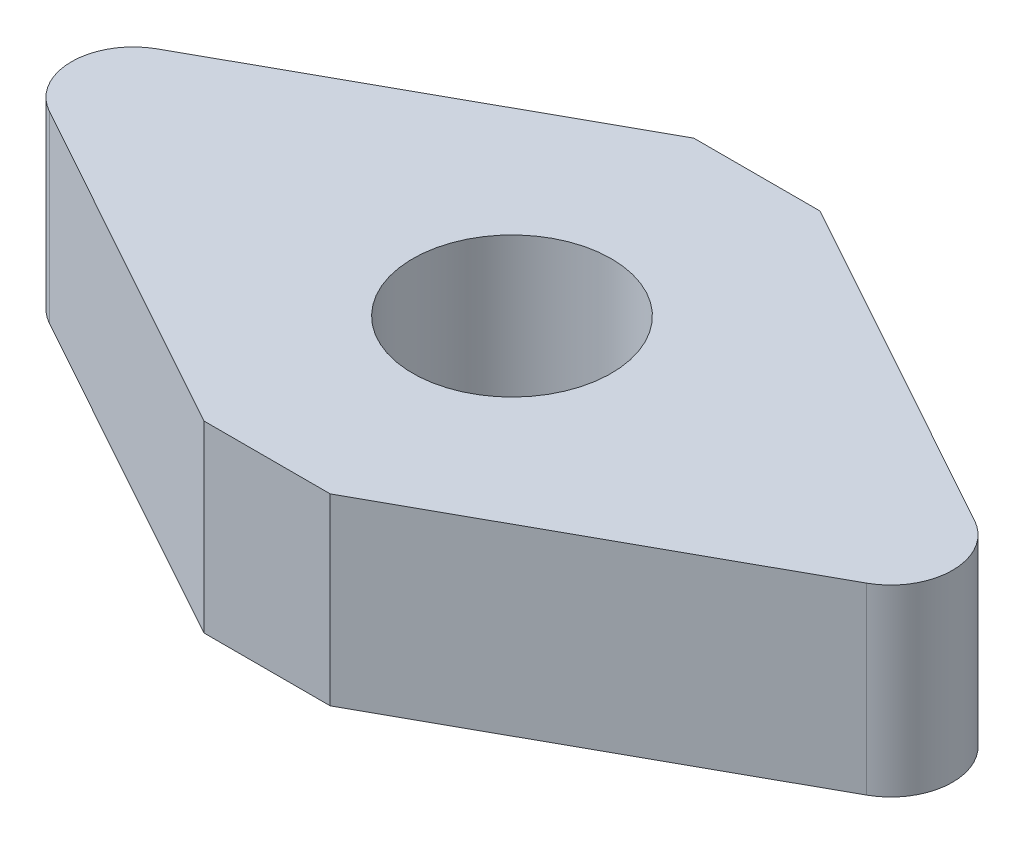
SolidWorks part; units mm, degrees
ref_plane "Ebene vorne" through (0, 0, 0) normal (0, 0, 1) x (1, 0, 0)
ref_plane "Ebene oben" through (0, 0, 0) normal (0, 1, 0) x (1, 0, 0)
ref_plane "Ebene rechts" through (0, 0, 0) normal (1, 0, 0) x (0, 0, -1)
sketch "Skizze1" plane through (0, 0, 0) normal (0, 1, 0) x (1, 0, 0)
  line L0 (1.6378, 6.35) -> (10.5946, 1.4004)
  line L1 (10.5946, -1.4004) -> (1.6378, -6.35)
  line L2 (-1.6378, -6.35) -> (-10.5946, -1.4004)
  line L3 (-10.5946, 1.4004) -> (-1.6378, 6.35)
  line L4 (0, -8.2296) -> (0, -4.3034) construction
  line L5 (0, -4.3034) -> (0, 9.0917) construction
  line L6 (-1.6378, 6.35) -> (1.6378, 6.35)
  line L7 (1.6378, -6.35) -> (-1.6378, -6.35)
  arc A1 (-10.5946, -1.4004) -> (-10.5946, 1.4004) centre (-9.8207, 0) cw
  arc A2 (10.5946, -1.4004) -> (10.5946, 1.4004) centre (9.8207, 0) ccw
  point P14 (13.1287, 0)
  dimension "D3" = 1.6
  dimension "D4" = 10.2334
  dimension "D5" = 10.2334
  dimension "D6" = 10.2334
  dimension "D7" = 10.2334
extrude "Aufsatz-Linear austragen1" add sketch "Skizze1" along normal blind 4.76
sketch "Skizze2" plane through (0, 0, 0) normal (0, -1, 0) x (-1, 0, 0)
  circle A0 centre (0, 0) radius 2.575
extrude "Schnitt-Linear austragen2" cut sketch "Skizze2" against normal blind 4.76
sketch "Skizze3" plane through (3.0713, 0, 5.5578) normal (0.4837, 0, 0.8752) x (0.8752, 0, -0.4837)
  line L0 (6.3155, 4.76) -> (6.3155, 0)
  line L1 (-1.6378, 4.76) -> (8.5956, 4.76) construction
  line L2 (-1.6378, 0) -> (8.5956, 0) construction
sketch "Skizze4" plane through (0, 4.76, 0) normal (0, 1, 0) x (1, 0, 0)
  line L1 (1.6378, -6.35) -> (10.5946, -1.4004) construction
  line L3 (10.4708, -1.4688) -> (8.6266, -2.4879)
sketch3d "3D-Skizze2"
  line L2 (0, 5.6069, 0.1012) -> (0, 5.6069, -6.302)
  line L3 (11.4207, 4.76, 0) -> (11.4207, 4.7116, 0)
  line L4 (11.4207, 4.7116, 0) -> (11.4207, 4.76, 0.005)
  line L5 (11.4207, 4.76, 0.005) -> (11.4207, 4.76, 0)
  arc A0 (10.5946, 4.76, 1.4004) -> (10.5946, 4.76, -1.4004) centre (9.8207, 4.76, 0) ccw construction
  point P8 (9.8207, 6.36, 0)
  dimension "D2" = 0.0484
  dimension "D3" = 0.005
